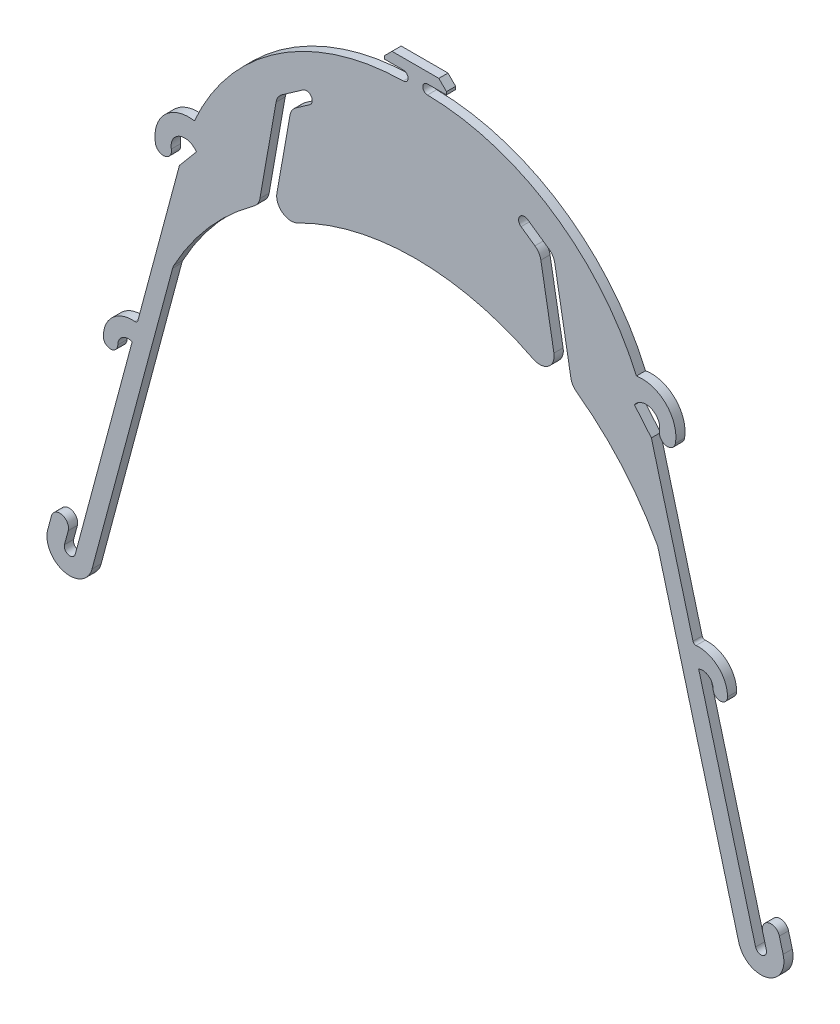
SolidWorks part; units mm, degrees
ref_plane "Front Plane" through (0, 0, 0) normal (0, 0, 1) x (1, 0, 0)
ref_plane "Top Plane" through (0, 0, 0) normal (0, 1, 0) x (1, 0, 0)
ref_plane "Right Plane" through (0, 0, 0) normal (1, 0, 0) x (0, 0, -1)
sketch "Sketch1" plane through (0, 0, 0) normal (0, 0, 1) x (1, 0, 0)
  line L0 (1108.8942, 3138.1387) -> (5028.4655, 3080.163) construction
  line L1 (-8.1, 0) -> (8.1, 0)
  line L2 (8.1, 0) -> (10.75, -2.65)
  line L3 (10.75, -2.65) -> (10.75, -3.65)
  line L4 (10.75, -3.65) -> (4.2, -3.65)
  line L6 (-46.1591, -32.0621) -> (-38.8472, -26.9422)
  line L10 (75.8, -64) -> (81.6464, -70.9674)
  line L11 (81.6464, -70.9674) -> (96.0444, -124.7014)
  line L14 (98, -132) -> (117.691, -205.488)
  line L16 (121.4228, -204.4881) -> (120.1287, -199.6584)
  line L17 (111.8955, -207.0409) -> (84.0105, -102.9726)
  line L19 (53.803, -66.9789) -> (48.2153, -35.2896)
  line L20 (46.1591, -32.0621) -> (38.8472, -26.9422)
  line L22 (0, 0) -> (0, -58) construction
  line L26 (-81.6464, -70.9674) -> (-96.0444, -124.7014)
  line L27 (-75.8, -64) -> (-81.6464, -70.9674)
  line L30 (-10.75, -3.65) -> (-4.2, -3.65)
  line L31 (-10.75, -2.65) -> (-10.75, -3.65)
  line L32 (-8.1, 0) -> (-10.75, -2.65)
  line L33 (36.5528, -30.2188) -> (41.3491, -33.5772)
  line L34 (43.4053, -36.8047) -> (47.924, -62.4318)
  line L36 (-36.5528, -30.2188) -> (-41.3491, -33.5772)
  line L37 (-111.8955, -207.0409) -> (-84.0105, -102.9726)
  line L38 (84.7798, -69.408) -> (81.6464, -70.9674) construction
  line L39 (-43.4053, -36.8047) -> (-47.924, -62.4318)
  line L40 (-53.803, -66.9789) -> (-48.2153, -35.2896)
  line L41 (125.9242, -198.1055) -> (127.2183, -202.9352)
  line L42 (123.0265, -198.882) -> (110.6014, -202.2113) construction
  line L43 (-125.9242, -198.1055) -> (-127.2183, -202.9352)
  line L44 (-121.4228, -204.4881) -> (-120.1287, -199.6584)
  line L45 (-98, -132) -> (-117.691, -205.488)
  arc A0 (4.2, -3.65) -> (4.1779, -6.9499) centre (4.2, -5.3) ccw
  arc A1 (4.1779, -6.9499) -> (76.4616, -55.0244) centre (3.1048, -86.9427) cw
  arc A2 (84.4494, -67.4762) -> (89.9609, -68.4662) centre (87.2, -68) ccw
  arc A3 (76.4616, -55.0244) -> (89.9609, -68.4662) centre (78.4538, -66.5231) cw
  arc A4 (75.8, -64) -> (84.4494, -67.4762) centre (79.7833, -66.5877) cw
  arc A5 (102.9776, -135.4) -> (107.9776, -135.4) centre (105.4776, -135.4) ccw
  arc A6 (102.9776, -135.4) -> (98, -132) centre (99.3276, -135.4) ccw
  arc A14 (40.7357, -67.7579) -> (47.924, -62.4318) centre (43, -63.3) ccw
  arc A15 (40.7357, -67.7579) -> (0, -58) centre (-0.0222, -148) ccw
  arc A16 (38.8472, -26.9422) -> (36.5528, -30.2188) centre (37.7, -28.5805) ccw
  arc A17 (97.0982, -125.4387) -> (107.9776, -135.4) centre (97.9776, -135.4) cw
  arc A18 (96.0444, -124.7014) -> (97.0982, -125.4387) centre (97.0103, -124.4426) ccw
  arc A19 (-96.0444, -124.7014) -> (-97.0982, -125.4387) centre (-97.0103, -124.4426) cw
  arc A20 (-97.0982, -125.4387) -> (-107.9776, -135.4) centre (-97.9776, -135.4) ccw
  arc A21 (-38.8472, -26.9422) -> (-36.5528, -30.2188) centre (-37.7, -28.5805) cw
  arc A22 (-40.7357, -67.7579) -> (0, -58) centre (0.0222, -148) cw
  arc A23 (-40.7357, -67.7579) -> (-47.924, -62.4318) centre (-43, -63.3) cw
  arc A31 (-102.9776, -135.4) -> (-98, -132) centre (-99.3276, -135.4) cw
  arc A32 (-102.9776, -135.4) -> (-107.9776, -135.4) centre (-105.4776, -135.4) cw
  arc A33 (-75.8, -64) -> (-84.4494, -67.4762) centre (-79.7833, -66.5877) ccw
  arc A34 (-76.4616, -55.0244) -> (-89.9609, -68.4662) centre (-78.4538, -66.5231) ccw
  arc A35 (-84.4494, -67.4762) -> (-89.9609, -68.4662) centre (-87.2, -68) cw
  arc A37 (-4.2, -3.65) -> (-4.1779, -6.9499) centre (-4.2, -5.3) cw
  arc A38 (-4.1779, -6.9499) -> (-76.4616, -55.0244) centre (-3.1048, -86.9427) ccw
  arc A39 (83.5798, -101.8898) -> (55.7906, -70.1576) centre (0, -147.0498) ccw
  arc A40 (84.0105, -102.9726) -> (83.5798, -101.8898) centre (79.1808, -104.2666) ccw
  arc A41 (55.7906, -70.1576) -> (53.803, -66.9789) centre (58.727, -66.1107) cw
  arc A42 (-83.5798, -101.8898) -> (-55.7906, -70.1576) centre (0, -147.0498) cw
  arc A43 (-84.0105, -102.9726) -> (-83.5798, -101.8898) centre (-79.1808, -104.2666) cw
  arc A44 (-55.7906, -70.1576) -> (-53.803, -66.9789) centre (-58.727, -66.1107) ccw
  arc A45 (48.2153, -35.2896) -> (46.1591, -32.0621) centre (43.2912, -36.1578) ccw
  arc A46 (41.3491, -33.5772) -> (43.4053, -36.8047) centre (38.4813, -37.673) cw
  arc A47 (-43.4053, -36.8047) -> (-41.3491, -33.5772) centre (-38.4813, -37.673) cw
  arc A48 (-46.1591, -32.0621) -> (-48.2153, -35.2896) centre (-43.2912, -36.1578) ccw
  arc A50 (117.691, -205.488) -> (121.4228, -204.4881) centre (119.5569, -204.988) ccw
  arc A51 (120.1287, -199.6584) -> (125.9242, -198.1055) centre (123.0265, -198.882) cw
  arc A52 (111.8955, -207.0409) -> (127.2183, -202.9352) centre (119.5569, -204.988) ccw
  arc A53 (-111.8955, -207.0409) -> (-127.2183, -202.9352) centre (-119.5569, -204.988) cw
  arc A54 (-120.1287, -199.6584) -> (-125.9242, -198.1055) centre (-123.0265, -198.882) ccw
  arc A55 (-117.691, -205.488) -> (-121.4228, -204.4881) centre (-119.5569, -204.988) cw
  point P31 (112.5853, -199.9739)
  point P34 (0, 0)
  point P41 (110.9322, -203.4459)
  point P112 (83.8607, -102.4137)
  point P115 (54.1593, -69)
  point P123 (47.8556, -33.25)
  point P126 (43.0457, -34.7651)
  point P129 (-43.0457, -34.7651)
  point P132 (-47.8556, -33.25)
  point P134 (84.7798, -69.408)
  dimension "D3" = 90
  dimension "D4" = 5
  dimension "D6" = 2
  dimension "D9" = 43
  dimension "D10" = 6
  dimension "D20" = 5
  dimension "D24" = 119.5569
  dimension "D27" = 2.5
  dimension "D28" = 10
  dimension "D29" = 1
  dimension "D30" = 3.65
  dimension "D37" = 4.75
  dimension "D38" = 11.67
  dimension "D39" = 2.8
  dimension "D43" = 80
  dimension "D7" = 9
  dimension "D16" = 95
  dimension "D18" = 5
  dimension "D19" = 5
  dimension "D41" = 3.928
  dimension "D42" = 3.5
  dimension "D1" = 3920
  dimension "D2" = 15
  dimension "D8" = 5
  dimension "D11" = 55
  dimension "D12" = 10
  dimension "D13" = 33.25
  dimension "D14" = 63.3
  dimension "D15" = 37.7
  dimension "D17" = 69
  dimension "D21" = 3.8634
  dimension "D23" = 204.988
  dimension "D25" = 132
  dimension "D26" = 98
  dimension "D31" = 3.4
  dimension "D32" = 64
  dimension "D33" = 75.8
  dimension "D34" = 40
  dimension "D35" = 4
  dimension "D36" = 11.4
  dimension "D45" = 5.3
  dimension "D46" = 4.2
  dimension "D47" = 3.65
  dimension "D48" = 45
  dimension "D49" = 10.75
  dimension "D50" = 2.65
  dimension "D51" = 58
extrude "Boss-Extrude1" add sketch "Sketch1" along normal blind 3.175
